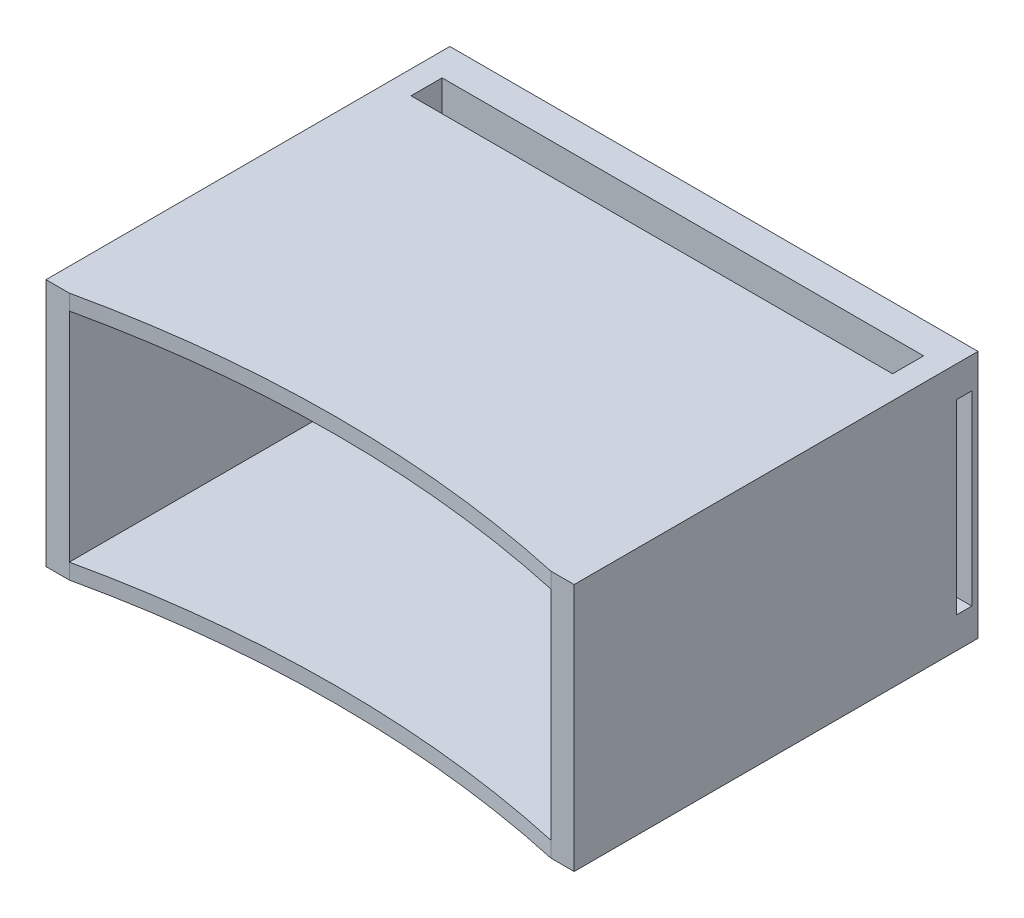
SolidWorks part; units mm, degrees
ref_plane "Front Plane" through (0, 0, 0) normal (0, 0, 1) x (1, 0, 0)
ref_plane "Top Plane" through (0, 0, 0) normal (0, 1, 0) x (1, 0, 0)
ref_plane "Right Plane" through (0, 0, 0) normal (1, 0, 0) x (0, 0, -1)
sketch "Sketch1" plane through (0, 0, 0) normal (0, 1, 0) x (1, 0, 0)
  line L1 (85, -45) -> (-85, -45)
  line L2 (85, -45) -> (85, 45)
  line L3 (85, 45) -> (-85, 45)
  line L4 (-85, -45) -> (-85, 45)
  line L5 (85, -45) -> (-85, 45) construction
  line L6 (85, 45) -> (-85, -45) construction
  point P0 (0, 0)
  dimension "D1" = 170
  dimension "D2" = 90
extrude "Boss-Extrude1" add sketch "Sketch1" along normal blind 80
sketch "Sketch3" plane through (0, 0, 45) normal (0, 0, 1) x (1, 0, 0)
  line L4 (-85, 0) -> (85, 0)
  line L5 (85, 0) -> (85, 80)
  line L6 (85, 80) -> (-85, 80)
  line L7 (-85, 80) -> (-85, 0)
  line L8 (-85, 0) -> (85, 0)
  line L9 (85, 0) -> (85, 80)
  line L10 (85, 80) -> (-85, 80)
  line L11 (-85, 80) -> (-85, 0)
  dimension "D1" = 0
extrude "Boss-Extrude3" add sketch "Sketch3" along normal blind 30
sketch "Sketch4" plane through (0, 80, 0) normal (0, 1, 0) x (1, 0, 0)
  line L1 (77.5, 35) -> (-77.5, 35)
  line L2 (77.5, 35) -> (77.5, 25)
  line L3 (77.5, 25) -> (-77.5, 25)
  line L4 (-77.5, 35) -> (-77.5, 25)
  line L5 (77.5, 35) -> (-77.5, 25) construction
  line L6 (77.5, 25) -> (-77.5, 35) construction
  line L7 (85, -45) -> (85, 45) construction
  line L8 (85, 45) -> (-85, 45) construction
  line L9 (-85, -45) -> (-85, 45) construction
  line L10 (85, -45) -> (85, 45)
  line L11 (85, 45) -> (-85, 45)
  line L12 (-85, -45) -> (-85, 45)
  point P0 (0, 30)
  dimension "D1" = 155
  dimension "D2" = 10
  dimension "D3" = 10
sketch "Sketch5" plane through (0, 0, 75) normal (0, 0, 1) x (1, 0, 0)
  line L1 (77.5, 5) -> (-77.5, 5)
  line L2 (77.5, 5) -> (77.5, 75)
  line L3 (77.5, 75) -> (-77.5, 75)
  line L4 (-77.5, 5) -> (-77.5, 75)
  line L5 (77.5, 5) -> (-77.5, 75) construction
  line L6 (77.5, 75) -> (-77.5, 5) construction
  line L7 (-85, 80) -> (-85, 0) construction
  point P0 (0, 40)
  point P9 (-85, 40)
  dimension "D1" = 155
  dimension "D2" = 70
extrude "Cut-Extrude3" cut sketch "Sketch5" against normal blind 110
extrude "Cut-Extrude4" cut sketch "Sketch4" against normal blind 75 contours L1 L4 L3 L2
sketch "Sketch6" plane through (0, 0, -35) normal (0, 0, 1) x (1, 0, 0)
  line L0 (77.5, 75) -> (-77.5, 75) construction
  line L1 (77.5, 75) -> (0, 75)
  line L2 (0, 107.6923) -> (0, -28.813) construction
  line L3 (-77.5, 5) -> (-76, 5)
  line L4 (-77.5, 80) -> (-77.5, 5)
  line L5 (-77.5, 5) -> (77.5, 5)
  line L6 (77.5, 5) -> (77.5, 80)
  line L7 (77.5, 80) -> (-77.5, 80)
  line L8 (-77.5, 75) -> (-77.5, 5)
  line L10 (77.5, 5) -> (77.5, 75)
  line L12 (-77.5, 5) -> (-77.5, 40)
  line L13 (-77.5, 40) -> (-76, 40)
  line L15 (-77.5, 5) -> (77.5, 5)
  line L16 (-76, 5) -> (-76, 40)
  line L17 (77.5, 5) -> (76, 5)
  line L18 (77.5, 5) -> (76, 5)
  line L19 (77.5, 41.6477) -> (77.5, 5)
  line L22 (77.5, 75) -> (77.5, 5)
  line L23 (76, 5) -> (76, 40)
  line L24 (77.5, 40) -> (76, 40)
  line M7 (77.5, 5) -> (77.5, 80)
  dimension "D2" = 76
  dimension "D3" = 35
  dimension "D1" = 0
sketch "Sketch7" plane through (0, 5, 0) normal (0, 1, 0) x (1, 0, 0)
  line L1 (76, 23) -> (-76, 23)
  line L3 (-76, 23) -> (76, 23)
  line L4 (-77.5, -75) -> (77.5, -75)
  line L12 (-76, 23) -> (-76, 19.5)
  line L13 (-76, 19.5) -> (76, 19.5)
  line L14 (76, 23) -> (76, 19.5)
  line L16 (-77.5, 35) -> (77.5, 35) construction
  line L17 (-77.5, -75) -> (77.5, -75)
  line L20 (77.5, 35) -> (-77.5, 35)
  line L27 (77.5, -75) -> (77.5, 35)
  line L28 (77.5, -75) -> (77.5, 35)
  line L31 (-77.5, 35) -> (-77.5, -75)
  line L32 (-77.5, 35) -> (-77.5, -75)
  point P11 (0, 19.5)
  dimension "D2" = 12
  dimension "D3" = 3.5
  dimension "D4" = 152
  dimension "D1" = 0
extrude "Boss-Extrude9" add sketch "Sketch6" along normal blind 15 contours L24 L23 L15 M7 | L16 L13 L12 L3
extrude "Boss-Extrude10" add sketch "Sketch7" along normal blind 5 contours L14 L1 L12 L13
sketch "Sketch10" plane through (0, 0, 75) normal (0, 0, 1) x (1, 0, 0)
  line L0 (85, 0) -> (85, 80) construction
  line L1 (-85, 0) -> (85, 0)
  line L2 (-85, 0) -> (-85, 80)
  line L3 (-85, 80) -> (85, 80)
  line L4 (85, 0) -> (85, 80)
  line L6 (-77.5, 5) -> (77.5, 5) construction
  line L7 (77.5, 5) -> (77.5, 75) construction
  line L8 (-77.5, 75) -> (-77.5, 5) construction
  line L9 (77.5, 75) -> (-77.5, 75) construction
  line L10 (-77.5, 5) -> (77.5, 5)
  line L11 (77.5, 5) -> (77.5, 75)
  line L12 (-77.5, 75) -> (-77.5, 5)
  line L13 (77.5, 75) -> (-77.5, 75)
  dimension "D1" = 80
extrude "Boss-Extrude13" add sketch "Sketch10" along normal blind 10
sketch "Sketch11" plane through (0, 80, 0) normal (0, 1, 0) x (1, 0, 0)
  line L0 (85, -85) -> (-85, -85) construction
  line L1 (77.5, -85) -> (-77.5, -85)
  line L3 (85, -85) -> (85, 45) construction
  arc A0 (-77.5, -85) -> (77.5, -85) centre (0, -436.559) cw
  dimension "D1" = 360
  dimension "D2" = 155
  dimension "D3" = 7.5
extrude "Cut-Extrude5" cut sketch "Sketch11" against normal through all
sketch "Sketch14" plane through (85, 0, 0) normal (1, 0, 0) x (0, 0, -1)
  line L13 (38, 70) -> (43, 70)
  line L14 (43, 70) -> (43, 10)
  line L15 (38, 10) -> (43, 10)
  line L16 (38, 70) -> (38, 10)
  line L17 (-85, 80) -> (45, 80) construction
  line L18 (45, 80) -> (45, 0) construction
  point P4 (45, 40)
  point P5 (43, 40)
  dimension "D1" = 60
  dimension "D2" = 5
  dimension "D3" = 2
extrude "Cut-Extrude6" cut sketch "Sketch14" against normal through all
sketch "Sketch15" plane through (0, 80, 0) normal (0, 1, 0) x (1, 0, 0)
  line L2 (85, -85) -> (85, -25)
  line L4 (-85, -85) -> (-85, -25)
  line L8 (85, -85) -> (85, 45) construction
  line L12 (-85, 45) -> (-85, -85) construction
  line L14 (0, 66.1615) -> (0, -94.617) construction
  line L15 (-122.7624, -25) -> (124.7748, -25) construction
  line L16 (85, 45) -> (-85, 45) construction
  line L17 (-77.5, -85) -> (-85, -85) construction
  circle A1 centre (-81.25, 21.25) radius 2.6
  circle A2 centre (81.25, 21.25) radius 2.6
  circle A3 centre (81.25, -71.25) radius 2.6
  circle A4 centre (-81.25, -71.25) radius 2.6
  dimension "D2" = 5.2
  dimension "D1" = 23.75
  dimension "D3" = 60
  dimension "D4" = 3.75
